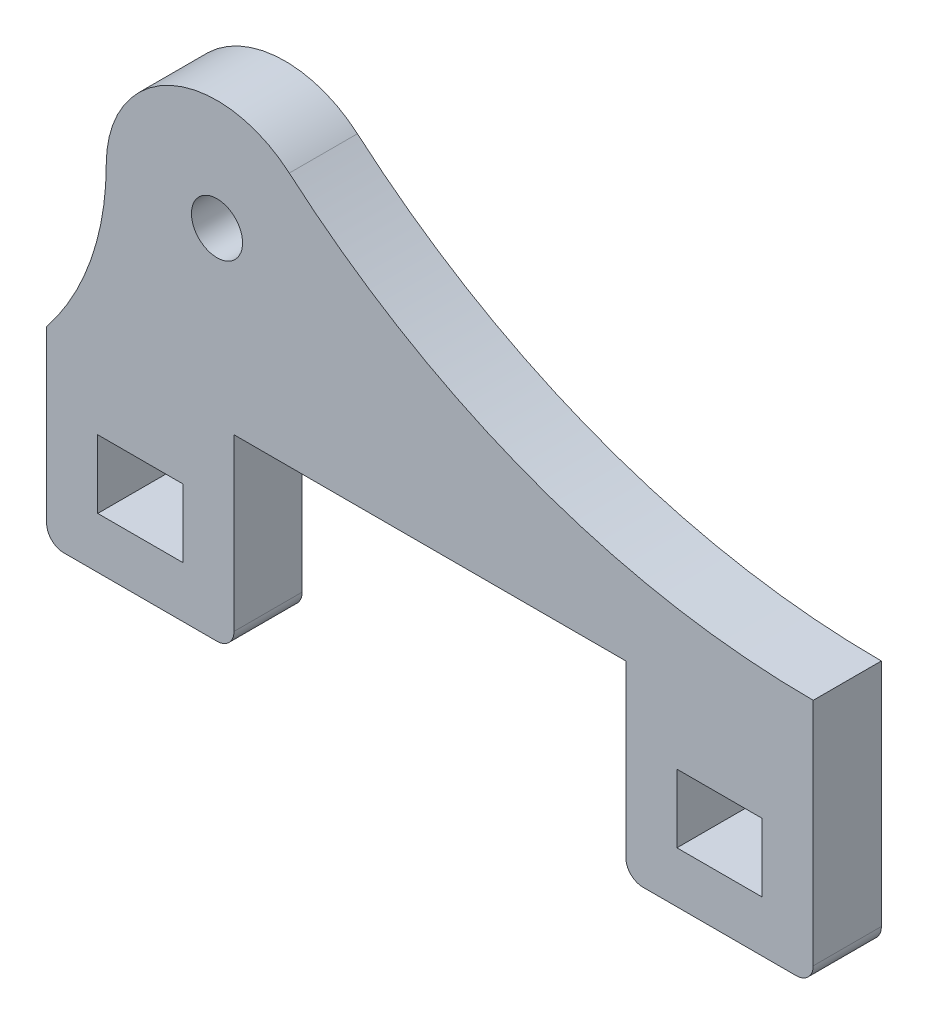
SolidWorks part; units mm, degrees
ref_plane "Front Plane" through (0, 0, 0) normal (0, 0, 1) x (1, 0, 0)
ref_plane "Top Plane" through (0, 0, 0) normal (0, 1, 0) x (1, 0, 0)
ref_plane "Right Plane" through (0, 0, 0) normal (1, 0, 0) x (0, 0, -1)
sketch "Sketch1" plane through (0, 0, 0) normal (0, 0, 1) x (1, 0, 0)
  line L0 (0, 0) -> (0, -11)
  line L1 (0, -11) -> (11, -11)
  line L2 (11, -11) -> (11, 0)
  line L3 (45, 0) -> (45, 3.5)
  line L4 (0, -4) -> (45, -4) construction
  line L5 (45, 3.5) -> (2.1236, 3.5) construction
  line L7 (11, 0) -> (34, 0)
  line L8 (34, 0) -> (34, -11)
  line L9 (34, -11) -> (45, -11)
  line L10 (45, -11) -> (45, 0)
  line L11 (3, -4) -> (8, -4)
  line L12 (3, -4) -> (3, -8)
  line L13 (3, -8) -> (8, -8)
  line L14 (8, -4) -> (8, -8)
  line L15 (37, -4) -> (42, -4)
  line L16 (37, -4) -> (37, -8)
  line L17 (37, -8) -> (42, -8)
  line L18 (42, -4) -> (42, -8)
  circle A0 centre (10, 10) radius 1.5
  circle A1 centre (10, 10) radius 6.5
  arc A2 (45, 3.5) -> (14.2432, 14.924) centre (45, 50.6154) cw
  arc A3 (3.5, 10) -> (0, 0) centre (-12.5357, 10) cw
  point P28 (5.5, -8)
  point P29 (5.5, -11)
  point P30 (39.5, -11)
  point P31 (39.5, -8)
  dimension "D8" = 3
  dimension "D9" = 5
  dimension "D2" = 11
  dimension "D3" = 11
  dimension "D4" = 45
  dimension "D5" = 11
  dimension "D6" = 10
  dimension "D7" = 10
  dimension "D11" = 4
  dimension "D12" = 5
  dimension "D13" = 4
extrude "Boss-Extrude1" add sketch "Sketch1" along normal blind 4
fillet "Fillet3" radius 1 4 edges at (45, -11, 2) (34, -11, 2) (0, -11, 2) (11, -11, 2)
